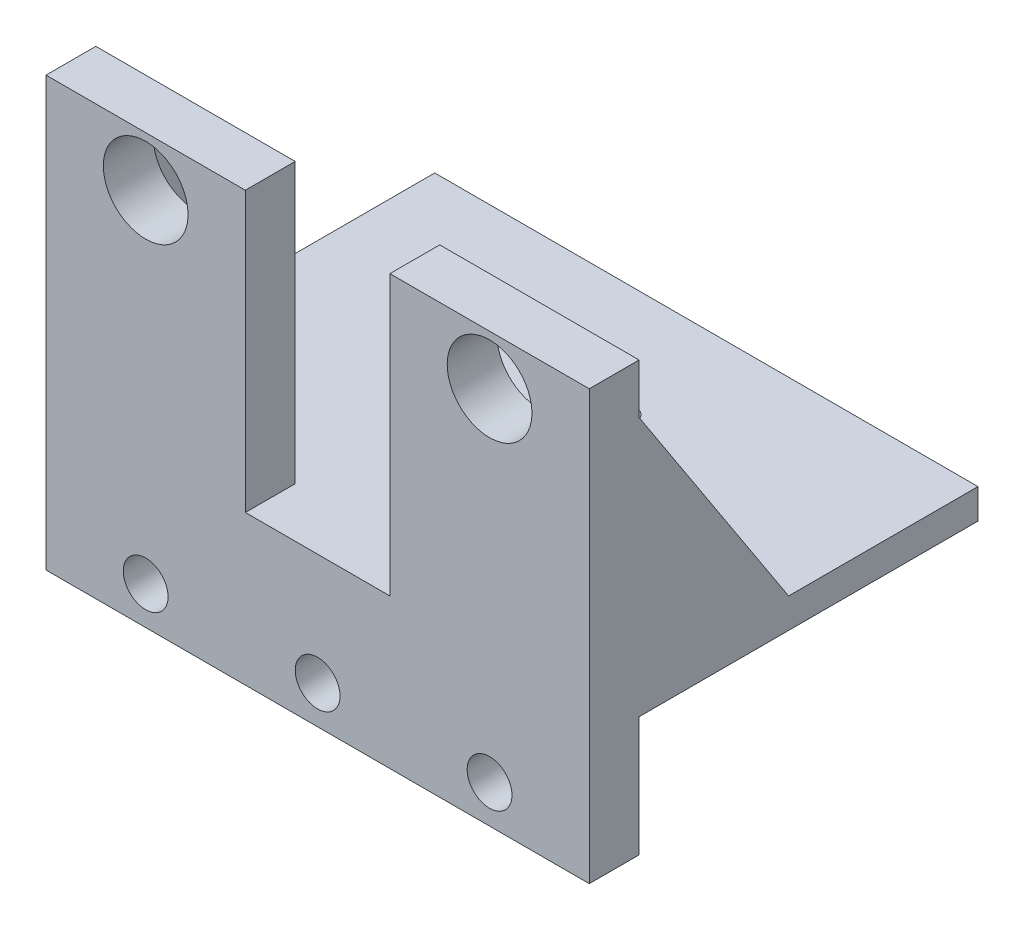
SolidWorks part; units mm, degrees
ref_plane "Front Plane" through (0, 0, 0) normal (0, 0, 1) x (1, 0, 0)
ref_plane "Top Plane" through (0, 0, 0) normal (0, 1, 0) x (1, 0, 0)
ref_plane "Right Plane" through (0, 0, 0) normal (1, 0, 0) x (0, 0, -1)
sketch "Sketch1" plane through (0, 0, 0) normal (0, 1, 0) x (1, 0, 0)
  line L1 (-40.6495, -11.3707) -> (13.8505, -11.3707)
  line L2 (-40.6495, -11.3707) -> (-40.6495, 27.6293)
  line L3 (-40.6495, 27.6293) -> (13.8505, 27.6293)
  line L4 (13.8505, -11.3707) -> (13.8505, 27.6293)
  dimension "D1" = 54.5
  dimension "D2" = 39
extrude "Boss-Extrude1" add sketch "Sketch1" along normal blind 3
sketch "Sketch10" plane through (0, 3, 0) normal (0, 1, 0) x (1, 0, 0)
  line L1 (13.8505, -11.3707) -> (13.8505, 27.6293) construction
  line L2 (-40.6495, -11.3707) -> (13.8505, -11.3707) construction
  circle A0 centre (-10.1495, 8.1293) radius 7
  dimension "D1" = 24
  dimension "D2" = 19.5
extrude "Cut-Extrude1" cut sketch "Sketch10" against normal blind 5 contours A0
hole_wizard "M2 Clearance Hole1" positions "3DSketch1" profile "Sketch11" hole size "M2" standard "ANSI Metric"
sketch3d "3DSketch1"
  line L0 (13.8505, 3, 11.3707) -> (13.8505, 3, -27.6293) construction
  line L1 (-40.6495, 3, 11.3707) -> (13.8505, 3, 11.3707) construction
  line L2 (-40.6495, 3, -27.6293) -> (-40.6495, 3, 11.3707) construction
  point P0 (-10.1495, 3, -0.1293)
  point P2 (-2.1548, 3, -8.1293)
  point P4 (-18.1443, 3, -8.1293)
  point P6 (-10.1495, 3, -16.1293)
  dimension "D1" = 16
  dimension "D2" = 11.31
  dimension "D3" = 11.31
  dimension "D4" = 11.31
  dimension "D5" = 11.31
  dimension "D6" = 24
  dimension "D7" = 24
  dimension "D8" = 11.5
  dimension "D9" = 16.0052
  dimension "D10" = 22.5052
sketch "Sketch11" plane through (-10.1495, 3, -0.1293) normal (1, 0, 0) x (0, 0, 1)
  line L0 (0, 0) -> (0, 17.721)
  line L1 (0, 17.721) -> (1.2, 17)
  line L2 (1.2, 17) -> (1.2, 0)
  line L5 (1.2, 0) -> (0, 0)
  line L10 (0, 17.721) -> (-1.2, 17) construction
  line L11 (0, -6.35) -> (0, 107.95) construction
  dimension "Hole Dia." = 2.4
  dimension "Hole Depth" = 17
  dimension "Drill Angle" = 118
sketch "Sketch12" plane through (0, 3, 0) normal (0, 1, 0) x (1, 0, 0)
  line L1 (13.8505, -11.3707) -> (-6.1495, -11.3707)
  line L2 (13.8505, -11.3707) -> (13.8505, -6.3707)
  line L3 (13.8505, -6.3707) -> (-6.1495, -6.3707)
  line L4 (-6.1495, -11.3707) -> (-6.1495, -6.3707)
  line L5 (-40.6495, -11.3707) -> (-20.6495, -11.3707)
  line L6 (-40.6495, -11.3707) -> (-40.6495, -6.3707)
  line L7 (-40.6495, -6.3707) -> (-20.6495, -6.3707)
  line L8 (-20.6495, -11.3707) -> (-20.6495, -6.3707)
  dimension "D1" = 20
  dimension "D2" = 20
  dimension "D3" = 5
  dimension "D4" = 5
extrude "Boss-Extrude2" add sketch "Sketch12" along normal blind 28
sketch "Sketch13" plane through (0, 0, 6.3707) normal (0, 0, -1) x (-1, 0, 0)
  line L1 (-13.8505, 31) -> (-13.8505, 3) construction
  line L2 (40.6495, 31) -> (40.6495, 3) construction
  line L3 (-13.8505, 3) -> (6.1495, 3) construction
  line L4 (20.6495, 3) -> (40.6495, 3) construction
  circle A0 centre (-3.8505, 26) radius 4.25
  circle A1 centre (30.6495, 26) radius 4.25
  dimension "D1" = 10
  dimension "D2" = 10
  dimension "D3" = 23
  dimension "D4" = 23
extrude "Cut-Extrude2" cut sketch "Sketch13" against normal blind 5
sketch "Sketch16" plane through (0, 0, 0) normal (0, -1, 0) x (1, 0, 0)
  line L0 (13.8505, 11.3707) -> (13.8505, -27.6293) construction
  line L1 (-40.6495, 11.3707) -> (13.8505, 11.3707)
  line L2 (-40.6495, 11.3707) -> (-40.6495, 6.3707)
  line L3 (-40.6495, 6.3707) -> (13.8505, 6.3707)
  line L4 (13.8505, 11.3707) -> (13.8505, 6.3707)
  dimension "D1" = 5
extrude "Boss-Extrude4" add sketch "Sketch16" along normal blind 12
hole_wizard "#8 Clearance Hole1" positions "3DSketch2" profile "Sketch17" hole size "#8" standard "ANSI Inch"
sketch3d "3DSketch2"
  line L1 (13.8505, 31, 11.3707) -> (13.8505, -12, 11.3707) construction
  line L2 (-40.6495, 31, 11.3707) -> (-40.6495, -12, 11.3707) construction
  line L4 (13.8505, -12, 11.3707) -> (-40.6495, -12, 11.3707) construction
  point P0 (-30.6495, -8.2, 11.3707)
  point P2 (-13.3995, -8.2, 11.3707)
  point P4 (3.8505, -8.2, 11.3707)
  dimension "D2" = 10
  dimension "D1" = 27.25
  dimension "D3" = 10
  dimension "D4" = 3.8
  dimension "D5" = 3.8
  dimension "D6" = 3.8
sketch "Sketch17" plane through (-30.6495, -8.2, 11.3707) normal (1, 0, 0) x (0, -1, 0)
  line L0 (0, 0) -> (0, 18.3507)
  line L1 (0, 18.3507) -> (2.2479, 17)
  line L2 (2.2479, 17) -> (2.2479, 0)
  line L5 (2.2479, 0) -> (0, 0)
  line L10 (0, 18.3507) -> (-2.2479, 17) construction
  line L11 (0, -6.35) -> (0, 107.95) construction
  dimension "Hole Dia." = 4.4958
  dimension "Hole Depth" = 17
  dimension "Drill Angle" = 118
sketch "Sketch20" plane through (13.8505, 0, 0) normal (1, 0, 0) x (0, 0, -1)
  line L0 (-6.3707, 26) -> (8.6293, 3)
  line L1 (-6.3707, 31) -> (-6.3707, 3) construction
  line L2 (-6.3707, 3) -> (27.6293, 3) construction
  dimension "D1" = 5
  dimension "D2" = 15
rib "Rib2" sketch "Sketch20" sketch "Sketch20" thickness 5 extrusion direction parallel to sketch draft on no parameters "D1"=5
sketch "Sketch21" plane through (-40.6495, 0, 0) normal (-1, 0, 0) x (0, 0, 1)
  line L0 (6.3707, 26) -> (-8.6293, 3)
  line L1 (6.3707, 31) -> (6.3707, 3) construction
  line L2 (-27.6293, 3) -> (6.3707, 3) construction
  dimension "D1" = 5
  dimension "D2" = 15
rib "Rib4" sketch "Sketch21" sketch "Sketch21" thickness 5 extrusion direction parallel to sketch draft on no parameters "D1"=5
